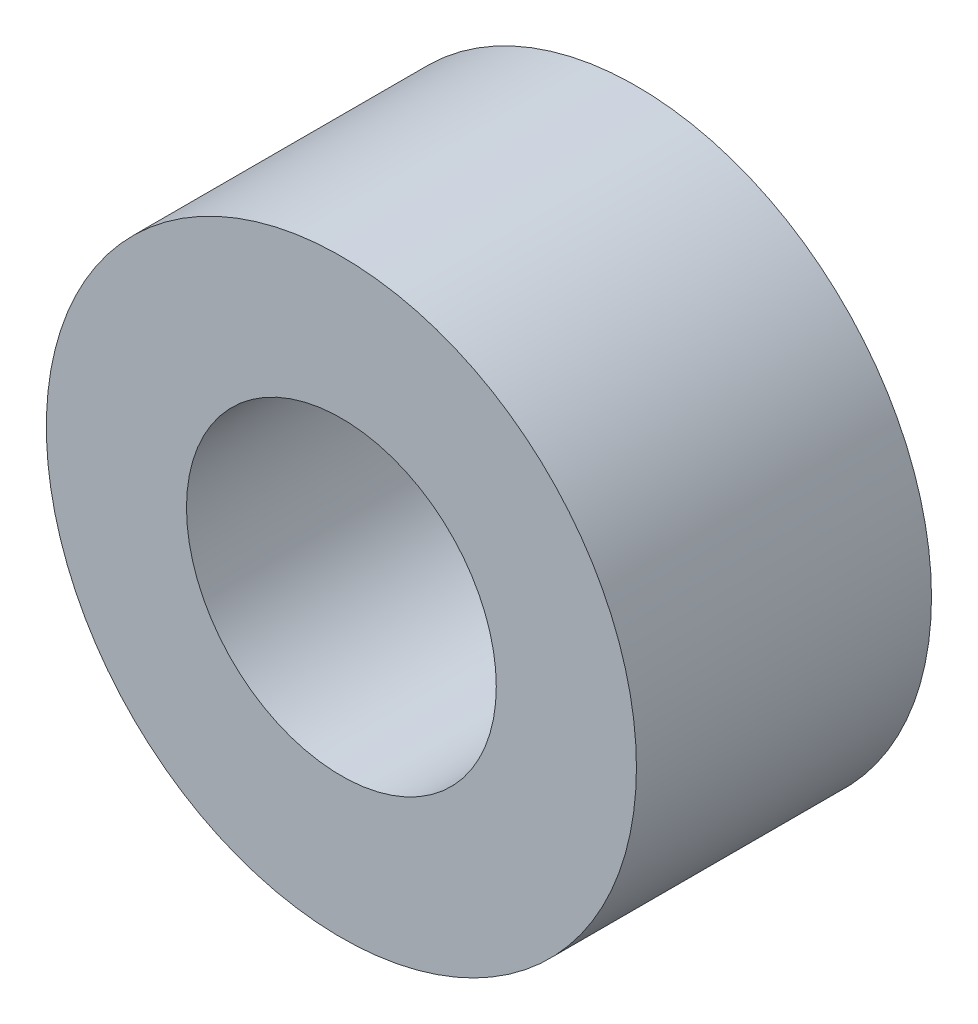
SolidWorks part; units mm, degrees
material "ABS"
ref_plane "Front Plane" through (0, 0, 0) normal (0, 0, 1) x (1, 0, 0)
ref_plane "Top Plane" through (0, 0, 0) normal (0, 1, 0) x (1, 0, 0)
ref_plane "Right Plane" through (0, 0, 0) normal (1, 0, 0) x (0, 0, -1)
sketch "Sketch1" plane through (0, 0, 0) normal (0, 0, 1) x (1, 0, 0)
  line L0 (0, 2.1) -> (0, 4) construction
  line L1 (0, -2.1) -> (0, -4) construction
  circle A0 centre (0, 0) radius 4
  circle A1 centre (0, 0) radius 2.1
  dimension "OD" = 8
  dimension "ID" = 4.2
sketch "Sketch2" plane through (0, 0, 0) normal (1, 0, 0) x (0, 0, -1)
  line L0 (-2, 2.1) -> (2, 2.1) construction
  line L1 (-2, -2.1) -> (2, -2.1) construction
  line L2 (-2, -4) -> (2, -4) construction
  line L3 (-2, 4) -> (2, 4) construction
  dimension "Length" = 4
extrude "Extrude1" add sketch "Sketch1" along normal up to vertex (2 mm away) and the other way up to vertex (2 mm away) up to point (0, 2.1, 2) other way up to point (0, 2.1, -2)
sketch "Sketch3" plane through (0, 0, 2) normal (0, 0, 1) x (1, 0, 0)
  circle A0 centre (0, 0) radius 2.1 construction
  circle A3 centre (0, 0) radius 2.1
  point P3 (-2.1, 0)
